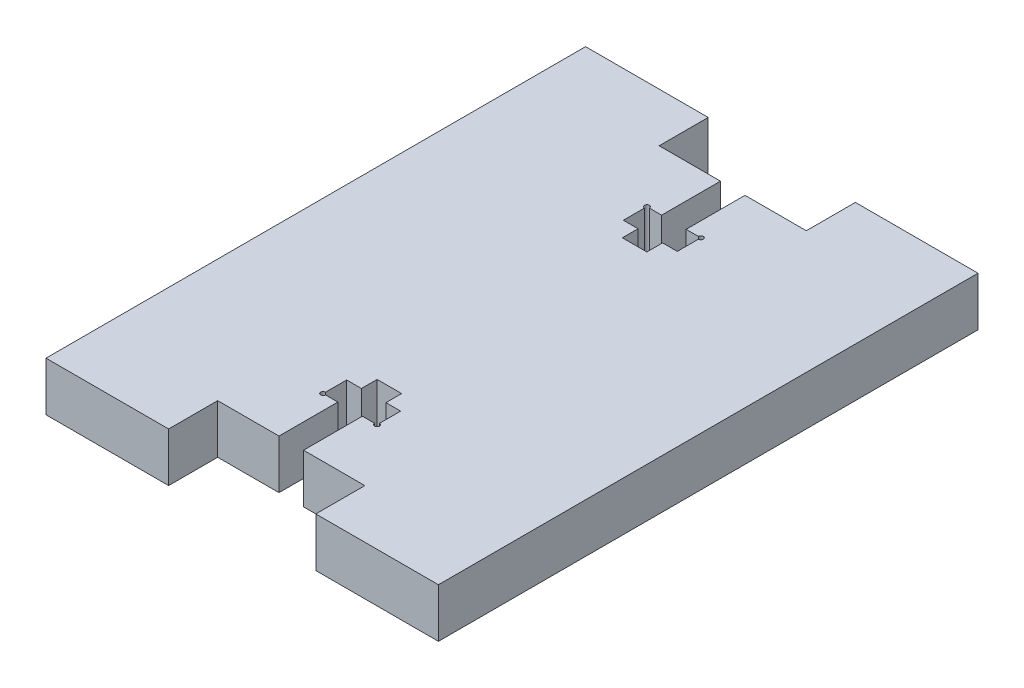
SolidWorks part; units mm, degrees
material "PVC rigido"
ref_plane "Piano frontale" through (0, 0, 0) normal (0, 0, 1) x (1, 0, 0)
ref_plane "Piano superiore" through (0, 0, 0) normal (0, 1, 0) x (1, 0, 0)
ref_plane "Piano destro" through (0, 0, 0) normal (1, 0, 0) x (0, 0, -1)
sketch "Schizzo1" plane through (0, 0, 0) normal (0, 1, 0) x (1, 0, 0)
  line L1 (-54.5649, -28.2811) -> (-14.5649, -28.2811)
  line L2 (-54.5649, -28.2811) -> (-54.5649, 26.7189)
  line L3 (-54.5649, 26.7189) -> (-14.5649, 26.7189)
  line L4 (-14.5649, -28.2811) -> (-14.5649, 26.7189)
  dimension "D1" = 40
  dimension "D2" = 55
sketch "Schizzo2" plane through (0, 0, 0) normal (0, 1, 0) x (1, 0, 0)
  line L0 (-54.5649, -0.7811) -> (-14.5649, -0.7811) construction
  line L5 (-54.5649, -28.2811) -> (-54.5649, 26.7189) construction
  line L6 (-14.5649, -28.2811) -> (-14.5649, 26.7189) construction
  line L7 (-34.5649, -28.2811) -> (-34.5649, 26.7189) construction
  line L8 (-54.5649, -28.2811) -> (-14.5649, -28.2811) construction
  line L9 (-54.5649, 26.7189) -> (-14.5649, 26.7189) construction
  line L22 (-42.0649, -28.2811) -> (-27.0649, -28.2811)
  line L23 (-42.0649, -28.2811) -> (-42.0649, -23.2811)
  line L24 (-42.0649, -23.2811) -> (-27.0649, -23.2811)
  line L25 (-27.0649, -28.2811) -> (-27.0649, -23.2811)
  line L26 (-42.0649, 26.7189) -> (-42.0649, 21.7189)
  line L27 (-42.0649, 21.7189) -> (-27.0649, 21.7189)
  line L28 (-27.0649, 26.7189) -> (-27.0649, 21.7189)
  line L29 (-42.0649, 26.7189) -> (-27.0649, 26.7189)
  point P33 (-34.5649, -23.2811)
  dimension "D3" = 15
  dimension "D4" = 5
extrude "Estrusione-Estrusione2" add sketch "Schizzo1" against normal blind 5
extrude "Taglio-Estrusione1" cut sketch "Schizzo2" against normal through all
sketch "Schizzo3" plane through (0, 0, 0) normal (0, 1, 0) x (1, 0, 0)
  line L1 (-35.8149, -23.2811) -> (-33.3149, -23.2811)
  line L2 (-54.5649, -0.7811) -> (-14.5649, -0.7811) construction
  line L3 (-54.5649, 26.7189) -> (-54.5649, -28.2811) construction
  line L15 (-14.5649, -28.2811) -> (-14.5649, 26.7189) construction
  line L19 (-34.5649, 21.7189) -> (-34.5649, -23.2811) construction
  line L20 (-42.0649, 21.7189) -> (-27.0649, 21.7189) construction
  line L21 (-27.0649, -23.2811) -> (-42.0649, -23.2811) construction
  line L26 (-35.8149, -23.2811) -> (-35.8149, -17.2811)
  line L27 (-35.8149, -17.2811) -> (-37.3149, -17.2811)
  line L28 (-37.3149, -17.2811) -> (-37.3149, -14.8811)
  line L29 (-37.3149, -14.8811) -> (-35.8149, -14.8811)
  line L30 (-35.8149, -14.8811) -> (-35.8149, -13.2811)
  line L31 (-35.8149, -13.2811) -> (-33.3149, -13.2811)
  line L32 (-33.3149, -13.2811) -> (-33.3149, -14.8811)
  line L33 (-33.3149, -14.8811) -> (-31.8149, -14.8811)
  line L34 (-31.8149, -14.8811) -> (-31.8149, -17.2811)
  line L35 (-31.8149, -17.2811) -> (-33.3149, -17.2811)
  line L36 (-33.3149, -17.2811) -> (-33.3149, -23.2811)
  line L60 (-35.8149, 11.7189) -> (-33.3149, 11.7189)
  line L61 (-35.8149, 13.3189) -> (-35.8149, 11.7189)
  line L62 (-37.3149, 13.3189) -> (-35.8149, 13.3189)
  line L63 (-37.3149, 15.7189) -> (-37.3149, 13.3189)
  line L64 (-35.8149, 15.7189) -> (-37.3149, 15.7189)
  line L65 (-35.8149, 21.7189) -> (-35.8149, 15.7189)
  line L66 (-35.8149, 21.7189) -> (-33.3149, 21.7189)
  line L67 (-33.3149, 15.7189) -> (-33.3149, 21.7189)
  line L68 (-31.8149, 15.7189) -> (-33.3149, 15.7189)
  line L69 (-31.8149, 13.3189) -> (-31.8149, 15.7189)
  line L70 (-33.3149, 13.3189) -> (-31.8149, 13.3189)
  line L71 (-33.3149, 11.7189) -> (-33.3149, 13.3189)
  point P53 (-34.5649, -23.2811)
  dimension "D2" = 5.5
  dimension "D3" = 10
  dimension "D8" = 2.5
  dimension "D9" = 6
  dimension "D11" = 2.4
extrude "Taglio-Estrusione3" cut sketch "Schizzo3" against normal through all
sketch "Schizzo4" plane through (0, 0, 0) normal (0, 1, 0) x (1, 0, 0)
  circle A0 centre (-37.3149, -17.2811) radius 0.25
  circle A1 centre (-31.8149, -17.2811) radius 0.25
  circle A2 centre (-37.3149, 15.7189) radius 0.25
  circle A3 centre (-31.8149, 15.7189) radius 0.25
  dimension "D1" = 0.5
  dimension "D2" = 0.5
extrude "Taglio-Estrusione4" cut sketch "Schizzo4" against normal blind 10
